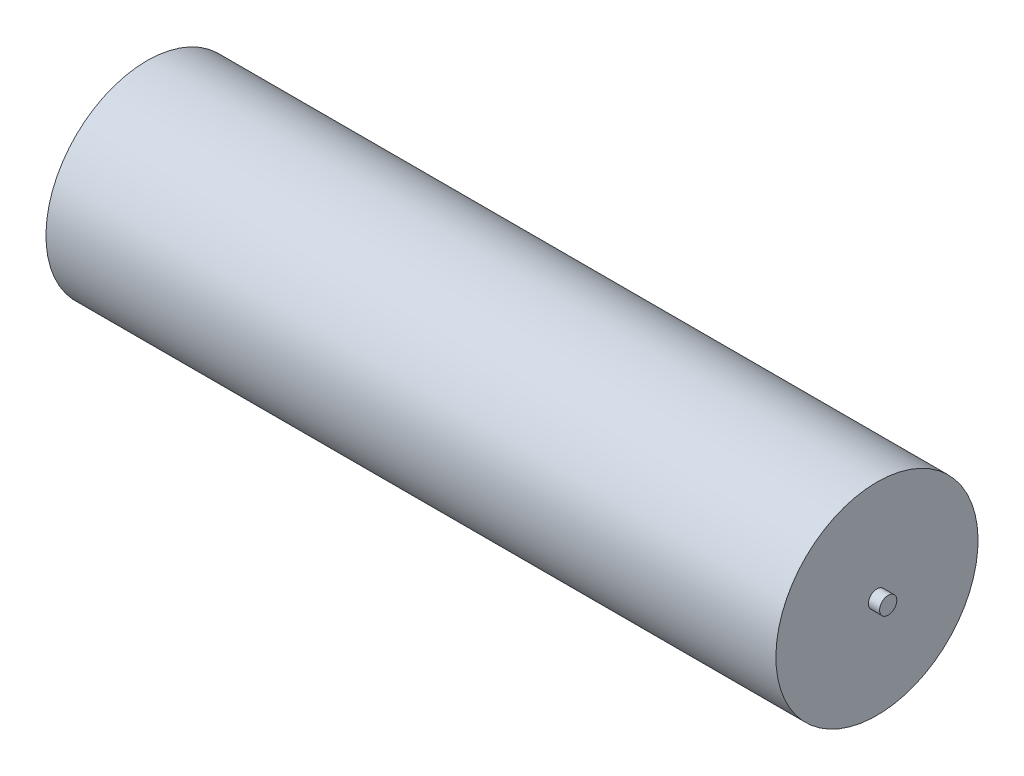
SolidWorks part; units mm, degrees
ref_plane "Ön Düzlem" through (0, 0, 0) normal (0, 0, 1) x (1, 0, 0)
ref_plane "Üst Düzlem" through (0, 0, 0) normal (0, 1, 0) x (1, 0, 0)
ref_plane "Sağ Düzlem" through (0, 0, 0) normal (1, 0, 0) x (0, 0, -1)
sketch "Sketch1" plane through (0, 0, 0) normal (0, 0, 1) x (1, 0, 0)
  line L0 (0, 0) -> (65, 0)
  line L1 (65, 0) -> (65, -9)
  line L2 (65, -9) -> (0, -9)
  line L3 (0, -9) -> (0, 0)
  dimension "D1" = 65
  dimension "D2" = 9
revolve "Revolve1" add sketch "Sketch1" angle 360 about L2
sketch "Sketch2" plane through (65, 0, 0) normal (1, 0, 0) x (0, 0, -1)
  circle A0 centre (0, -9) radius 0.7645
extrude "Boss-Extrude1" add sketch "Sketch2" along normal blind 1
